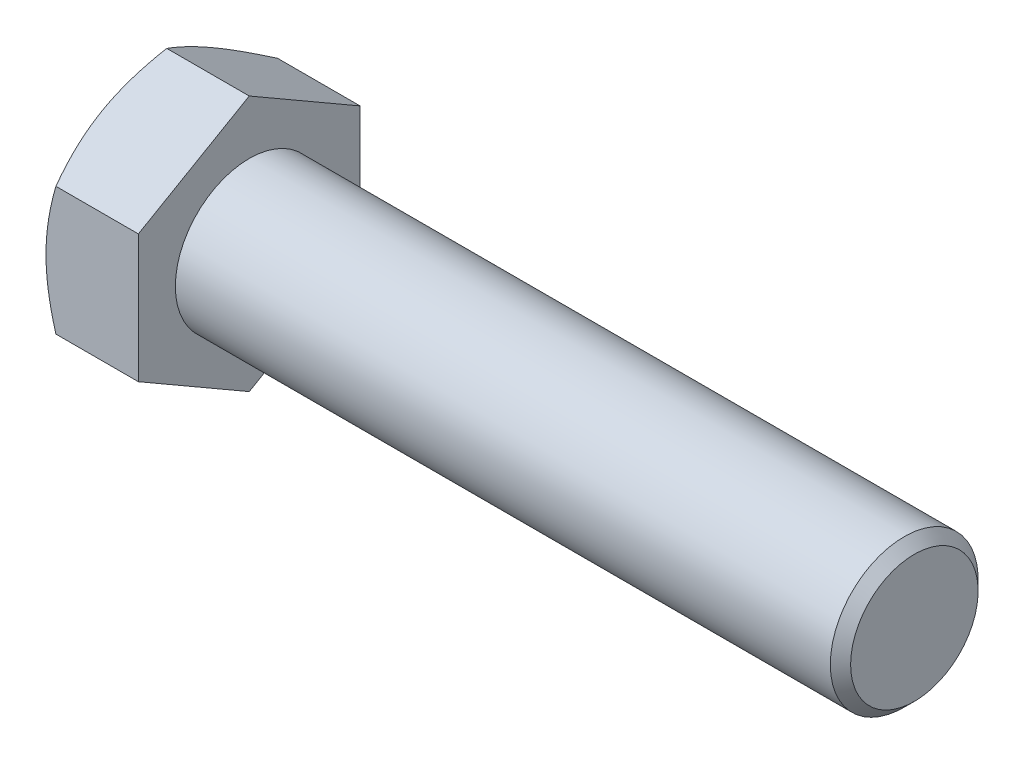
SolidWorks part; units mm, degrees
extrude "BaseHead" add sketch "Sketch1" along normal blind 12.5
sketch "Sketch1" plane through (0, 0, 0) normal (1, 0, 0) x (0, 0, -1)
  line L0 (15, 8.6603) -> (15, -8.6603)
  line L1 (-15, 8.6603) -> (-15, -8.6603)
  line L2 (15, -8.6603) -> (0, -17.3205)
  line L3 (0, -17.3205) -> (-15, -8.6603)
  line L4 (15, 8.6603) -> (0, 17.3205)
  line L5 (0, 17.3205) -> (-15, 8.6603)
  dimension "D2" = 120
ref_plane "Plane1" through (0, 0, 0) normal (0, 0, 1) x (1, 0, 0)
ref_plane "Plane2" through (0, 0, 0) normal (0, 1, 0) x (1, 0, 0)
ref_plane "Plane3" through (0, 0, 0) normal (1, 0, 0) x (0, 0, -1)
sketch "BodySke" plane through (0, 0, 0) normal (0, 0, 1) x (1, 0, 0)
  line L1 (0, 0) -> (102.5, 0)
  line L2 (0, 0) -> (0, 10)
  line L4 (102.5, 0) -> (102.5, 8.626)
  line L5 (12.5, 17.3205) -> (12.5, 8.6603) construction
  line L6 (102.5, 8.626) -> (101.126, 10)
  line L7 (0, 0) -> (110.49, 0) construction
  line L8 (102.5, -8.626) -> (101.126, -10) construction
  line L9 (0, 8.6603) -> (0, -8.6603) construction
  line L10 (15, 15.24) -> (15, -1.27) construction
  line L11 (56.5, 15.24) -> (56.5, -1.27) construction
  line L12 (12.5, 8.6603) -> (12.5, -8.6603) construction
  line L15 (0, 10) -> (101.126, 10)
  dimension "Body_ch_ang" = 45
revolve "BaseBody" add sketch "BodySke" angle 360 about L7
cosmetic thread "ThreadCosmetic" [suppressed] parameters "Thread_length"=46, "Thread_minor"=17.252
fillet "HeadFillet" [suppressed] radius 0.8
sketch "Sketch3" plane through (0, 0, 0) normal (0, 0, 1) x (1, 0, 0)
  line L0 (0, 15) -> (4.2265, 22.3205)
  line L1 (0, 17.3205) -> (0, 8.6603) construction
  line L2 (4.2265, 22.3205) -> (4.2265, 27.3205)
  line L3 (4.2265, 27.3205) -> (-10, 27.3205)
  line L4 (-10, 27.3205) -> (-10, 15)
  line L5 (-10, 15) -> (0, 15)
  line L6 (0, 0) -> (99.06, 0) construction
  line L7 (12.5, 17.3205) -> (0, 17.3205) construction
  dimension "D2" = 5
  dimension "D3" = 10
  dimension "D4" = 5
  dimension "Head_ch_ang" = 30
revolve "HeadChamfer" cut sketch "Sketch3" angle 360 about L6
sketch "ThdSchSke" plane through (0, 0, 0) normal (0, 0, 1) x (1, 0, 0)
  line L0 (56.5, -8.626) -> (55.5379, -10)
  line L1 (56.5, -8.626) -> (57.4621, -10)
  line L2 (57.4621, -10) -> (57.4621, -12.5)
  line L3 (-3.175, 0) -> (5.1513, 0) construction
  line L5 (57.4621, -12.5) -> (55.5379, -12.5)
  line L6 (55.5379, -12.5) -> (55.5379, -10)
revolve "ThreadSchematic" [suppressed] cut sketch "ThdSchSke" angle 360 about L3
pattern_linear "ThdSchPat" [suppressed]
equation "\"D3@Sketch1\" = \"Width_flats@Sketch1\" / 2"
equation "\"D4@Sketch1\" = \"D3@Sketch1\""
equation "\"D5@Sketch1\" = \"D4@Sketch1\""
equation "\"Thread_minor@ThreadCosmetic\" = \"Minor_dia@BodySke\""
equation "\"D1@Sketch3\" = \"Width_flats@Sketch1\" / 2"
equation "\"Thread_length@ThreadCosmetic\" = ((sgn( (\"Length@BodySke\" - \"Advance@BodySke\" ) - \"Thread_nom@BodySke\" )-1)*( (\"Length@BodySke\" - \"Advance@BodySke\" ) - \"Thread_nom@BodySke\" ))/-2+ \"Thread_nom@BodySke\""
equation "\"Thread_minor@ThdSchSke\" = \"Minor_dia@BodySke\""
equation "\"Diameter@ThdSchSke\" = \"Diameter@BodySke\""
equation "\"Overcut@ThdSchSke\" = \"Diameter@BodySke\" * 1.25"
equation "\"Start@ThdSchSke\" = \"Head_ht@BaseHead\" + \"Length@BodySke\" - \"Thread_length@ThreadCosmetic\"  '---Non-countersunk---"
equation "\"Num_threads@ThdSchPat\" = int( \"Thread_length@ThreadCosmetic\" / \"Advance@BodySke\" + 0.999 )  + 1"
equation "\"Advance@ThdSchPat\" = \"Thread_length@ThreadCosmetic\" /  (\"Num_threads@ThdSchPat\" - 1) 'relax it"
equation "\"Num_threads@ThdSchPat\" = \"Num_threads@ThdSchPat\" - sgn( \"Num_threads@ThdSchPat\" - 1) '---chamfered tips only---"
